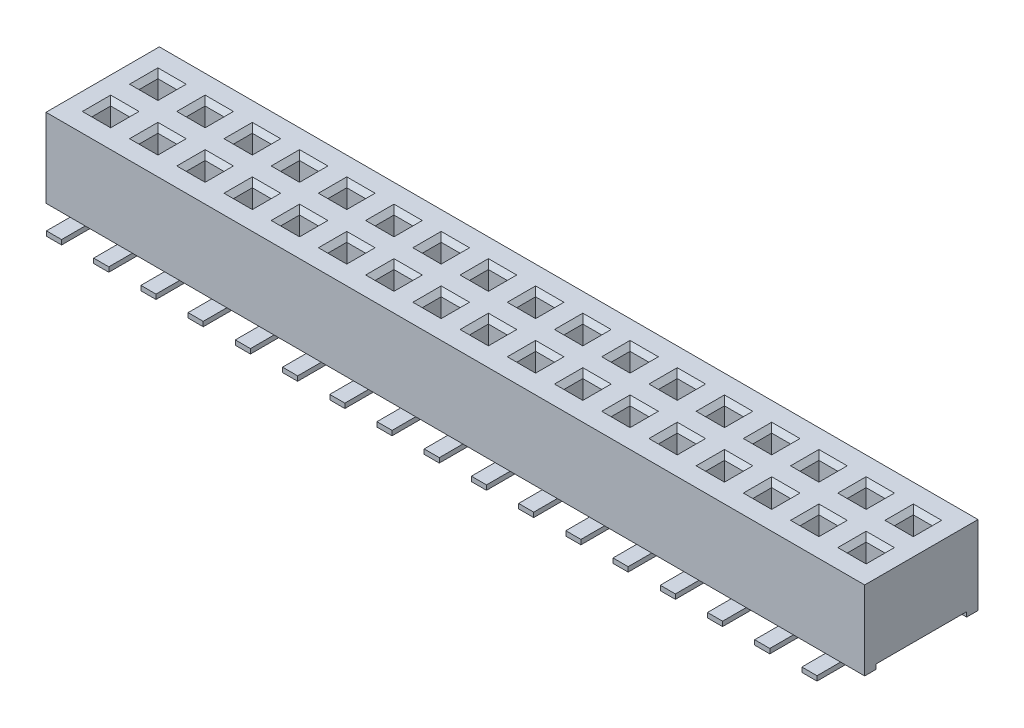
SolidWorks part; units mm, degrees
ref_plane "Front" through (0, 0, 0) normal (0, 0, 1) x (1, 0, 0)
ref_plane "Top" through (0, 0, 0) normal (0, 1, 0) x (1, 0, 0)
ref_plane "Right" through (0, 0, 0) normal (1, 0, 0) x (0, 0, -1)
sketch "Sketch1" plane through (0, 0, 0) normal (0, 1, 0) x (1, 0, 0)
  line L0 (-11.0109, -1.524) -> (11.0109, 1.524) construction
  line L1 (-11.0109, 1.524) -> (11.0109, 1.524)
  line L2 (-11.0109, 1.524) -> (-11.0109, -1.524)
  line L3 (-11.0109, -1.524) -> (11.0109, -1.524)
  line L4 (11.0109, 1.524) -> (11.0109, -1.524)
  dimension "D1" = 3.048
  dimension "D2" = 22.0218
extrude "Main Body" add sketch "Sketch1" along normal blind 2.1209
ref_plane "Plane2" through (10.16, 0, 0) normal (1, 0, 0) x (0, 0, -1)
extrude "Cut-Extrude2" cut sketch "Sketch6" against normal through all
sketch "Sketch6" plane through (11.0109, 0, 0) normal (1, 0, 0) x (0, 0, -1)
  line L1 (-1.524, 2.1209) -> (-1.524, 0) construction
  line L2 (-1.524, 0) -> (1.524, 0) construction
  line L3 (-1.2192, 0) -> (1.2192, 0)
  line L5 (-1.2192, 0.127) -> (-1.2192, 0)
  line L7 (-1.2192, 0.127) -> (1.2192, 0.127)
  line L9 (1.2192, 0.127) -> (1.2192, 0)
  line L12 (1.524, 2.1209) -> (1.524, 0) construction
  dimension "D2" = 0.3048
  dimension "D1" = 0.127
  dimension "D3" = 0.3048
sketch "Sketch2" plane through (0, 2.1209, 0) normal (0, 1, 0) x (-1, 0, 0)
  line L0 (0, 0) -> (-9.2157, 0) construction
  line L1 (-6.4241, -0.635) -> (-4.2326, -0.635) construction
  line L2 (-10.414, -0.381) -> (-9.906, -0.381)
  line L3 (-10.414, -0.381) -> (-10.414, -0.889)
  line L4 (-10.414, -0.889) -> (-9.906, -0.889)
  line L6 (-9.906, -0.381) -> (-9.906, -0.889)
  line L7 (-9.906, 0.381) -> (-9.906, 0.889)
  line L8 (-10.414, 0.889) -> (-9.906, 0.889)
  line L9 (-10.414, 0.381) -> (-10.414, 0.889)
  line L10 (-10.16, 1.9747) -> (-10.16, -2.1621) construction
  line L11 (-11.0109, 1.524) -> (-11.0109, -1.524) construction
  line L12 (-10.414, 0.381) -> (-9.906, 0.381)
  line L13 (-6.4241, 0.635) -> (-4.3872, 0.635) construction
  dimension "D1" = 1.27
  dimension "D2" = 0.508
  dimension "D3" = 0.508
  dimension "D4" = 0.8509
extrude "Cut-Extrude1" cut sketch "Sketch2" against normal blind 2.794
chamfer "Chamfer1" distance 0.127 distance2 0.127 8 edges at (10.414, 2.1209, -0.635) (10.16, 2.1209, -0.889) (9.906, 2.1209, -0.635) (10.16, 2.1209, -0.381) (10.16, 2.1209, 0.381) (9.906, 2.1209, 0.635) (10.16, 2.1209, 0.889) (10.414, 2.1209, 0.635)
pattern_linear "LPattern1" count 17 spacing 1.27 along (-1, 0, 0) of "Cut-Extrude1", "Chamfer1"
sketch "Sketch7" plane through (10.16, 0, 0) normal (1, 0, 0) x (0, 0, -1)
  line L0 (0, 0) -> (0, 2.2434) construction
  line L1 (-0.889, 0.635) -> (-0.889, 0.127)
  line L2 (-1.143, 0) -> (-2.159, 0)
  line L3 (-0.889, 0.127) -> (-0.889, 1.9939) construction
  line L4 (-1.016, 0.635) -> (-1.016, 0.127)
  line L5 (-2.159, 0) -> (-2.159, -0.127)
  line L6 (-1.143, -0.127) -> (-2.159, -0.127)
  line L7 (-1.524, 2.1209) -> (1.524, 2.1209) construction
  line L8 (-1.016, 0.635) -> (-0.889, 0.635)
  line L9 (1.016, 0.635) -> (0.889, 0.635)
  line L10 (1.143, -0.127) -> (2.159, -0.127)
  line L11 (2.159, 0) -> (2.159, -0.127)
  line L12 (1.016, 0.635) -> (1.016, 0.127)
  line L13 (1.143, 0) -> (2.159, 0)
  line L14 (0.889, 0.635) -> (0.889, 0.127)
  arc A0 (-0.889, 0.127) -> (-1.143, -0.127) centre (-1.143, 0.127) cw
  arc A1 (-1.016, 0.127) -> (-1.143, 0) centre (-1.143, 0.127) cw
  arc A2 (1.016, 0.127) -> (1.143, 0) centre (1.143, 0.127) ccw
  arc A3 (0.889, 0.127) -> (1.143, -0.127) centre (1.143, 0.127) ccw
  dimension "D2" = 0.254
  dimension "D1" = 2.2479
  dimension "D4" = 4.318
  dimension "D5" = 0.762
  dimension "D3" = 0.127
extrude "Lead Pin-D" add sketch "Sketch7" along normal mid plane 0.4064
pattern_linear "Lead Pattern-D" count 17 spacing 1.27 along (-1, 0, 0) of "Lead Pin-D"
sketch "Sketch30" plane through (10.16, 0, 0) normal (1, 0, 0) x (0, 0, -1)
  line L0 (-1.524, 2.1209) -> (1.524, 2.1209) construction
  line L1 (-2.4384, 2.1209) -> (-1.5748, 2.1209)
  line L2 (-2.4384, 2.1209) -> (-2.4384, 0.254)
  line L3 (-2.4384, 0.254) -> (-1.5748, 0.254)
  line L4 (-1.5748, 2.1209) -> (-1.5748, 0.254)
  line L5 (-1.524, 0) -> (-1.2192, 0) construction
  line L6 (-1.1684, 0) -> (-0.3048, 0)
  line L7 (-1.1684, 0) -> (-1.1684, 1.8669)
  line L8 (-1.1684, 1.8669) -> (-0.3048, 1.8669)
  line L9 (-0.3048, 0) -> (-0.3048, 1.8669)
  line L10 (-2.0066, 0.254) -> (-2.0066, 1.4535) construction
  line L12 (-0.7366, 1.8669) -> (-0.7366, 2.0625) construction
  line L14 (-1.3716, 0) -> (-1.3716, 3.8542) construction
  point P14 (-1.3716, 0)
  dimension "D1" = 0.254
  dimension "D3" = 0.8636
  dimension "D4" = 1.27
  dimension "D5" = 0.8636
  dimension "D6" = 0.254
sketch "Sketch10" plane through (11.0109, 0, 0) normal (1, 0, 0) x (0, 0, -1)
  line L0 (0, 3.5147) -> (0, -0.2313) construction
  line L1 (-1.7373, 1.0605) -> (1.6711, 1.0605) construction
  line L2 (-1.524, 2.1209) -> (-1.143, 2.1209)
  line L3 (-1.524, 2.1209) -> (1.524, 2.1209) construction
  line L4 (-1.0744, 2.1209) -> (0.16, 2.1209)
  line L5 (-1.524, 2.1209) -> (-1.524, 1.7399)
  line L6 (-1.524, 1.7399) -> (-1.143, 2.1209)
  line L7 (1.524, 1.7399) -> (1.143, 2.1209)
  line L8 (-1.524, 0) -> (-1.2192, 0) construction
  line L9 (1.524, 2.1209) -> (1.524, 1.7399)
  line L10 (1.524, 2.1209) -> (1.143, 2.1209)
  line L11 (-1.524, 0.381) -> (-1.143, 0)
  line L12 (-1.524, 0) -> (-1.524, 0.381)
  line L13 (-1.524, 0) -> (-1.143, 0)
  line L14 (0.16, 2.1209) -> (0.1016, 1.9939)
  line L15 (0.1016, 1.9939) -> (-1.016, 1.9939)
  line L16 (-1.016, 1.9939) -> (-1.0744, 2.1209)
  line L17 (-0.2057, 0) -> (-0.1372, 0.127)
  line L18 (-0.1372, 0.127) -> (0.9804, 0.127)
  line L19 (0.9804, 0.127) -> (1.049, 0)
  line L20 (-0.2057, 0) -> (1.049, 0)
  line L21 (-0.4572, 1.9939) -> (-0.4572, 2.4488) construction
  line L22 (1.524, 2.1209) -> (1.524, 0) construction
  line L23 (0.4216, 0.127) -> (0.4216, 0.4568) construction
  dimension "D2" = 0.381
  dimension "D3" = 0.0686
  dimension "D1" = 0.381
  dimension "D4" = 0.127
  dimension "D5" = 0.0584
  dimension "D6" = 1.1176
  dimension "D7" = 0.127
  dimension "D8" = 1.1176
  dimension "D9" = 0.0686
  dimension "D10" = 0.475
sketch "Sketch31" plane through (0, 0.127, 0) normal (0, -1, 0) x (1, 0, 0)
  line L0 (9.525, 0.3503) -> (9.525, -0.2523) construction
  line L1 (9.398, 0.1905) -> (9.4615, 0.1905)
  line L2 (9.398, 0.1905) -> (9.398, -0.1905)
  line L3 (9.398, -0.1905) -> (9.4615, -0.1905)
  line L4 (9.652, 0.1905) -> (9.652, -0.1905)
  line L5 (9.525, 0.3175) -> (9.525, -0.3175) construction
  line L6 (9.4615, 0.3175) -> (9.5885, 0.3175)
  line L7 (9.4615, 0.3175) -> (9.4615, 0.1905)
  line L8 (9.4615, -0.3175) -> (9.5885, -0.3175)
  line L9 (9.5885, 0.3175) -> (9.5885, 0.1905)
  line L10 (9.4615, -0.1905) -> (9.4615, -0.3175)
  line L11 (9.5885, -0.1905) -> (9.5885, -0.3175)
  line L12 (9.5885, 0.1905) -> (9.652, 0.1905)
  line L13 (9.5885, -0.1905) -> (9.652, -0.1905)
  line L14 (9.398, 0) -> (9.652, 0) construction
  line L15 (11.0109, -1.2192) -> (11.0109, 1.2192) construction
  dimension "D1" = 0.127
  dimension "D2" = 0.254
  dimension "D3" = 0.381
  dimension "D4" = 0.635
  dimension "D5" = 1.4859
sketch "Sketch32" plane through (0, 0.127, 0) normal (0, -1, 0) x (1, 0, 0)
  line L0 (9.525, 0.0889) -> (9.525, -0.0889) construction
  line L1 (9.2075, 0.0889) -> (9.8425, 0.0889)
  line L2 (9.2075, 0.0889) -> (9.2075, -0.0889)
  line L3 (9.2075, -0.0889) -> (9.8425, -0.0889)
  line L4 (9.8425, 0.0889) -> (9.8425, -0.0889)
  line L5 (9.525, 0.3503) -> (9.525, -0.2523) construction
  line L6 (9.2075, 0) -> (9.8425, 0) construction
  line L7 (9.398, 0) -> (9.652, 0) construction
  dimension "D1" = 0.635
  dimension "D2" = 0.1778
